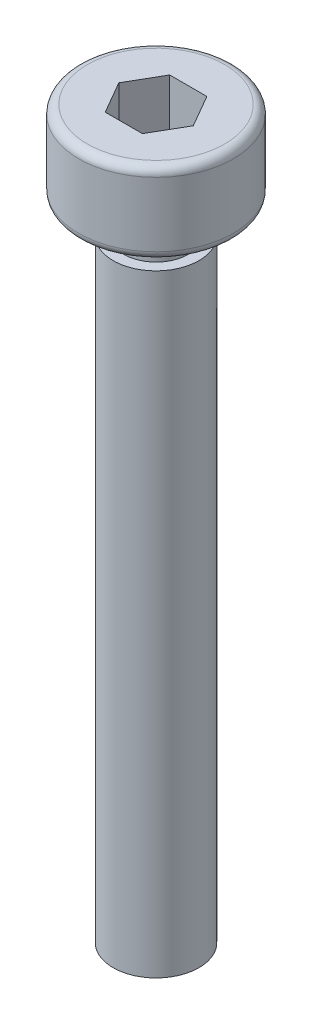
SolidWorks part; units mm, degrees
material "AISI 304"
ref_plane "前视基准面" through (0, 0, 0) normal (0, 0, 1) x (1, 0, 0)
ref_plane "上视基准面" through (0, 0, 0) normal (0, 1, 0) x (1, 0, 0)
ref_plane "右视基准面" through (0, 0, 0) normal (1, 0, 0) x (0, 0, -1)
sketch "草图1" plane through (0, 0, 0) normal (0, 0, 1) x (1, 0, 0)
  line L0 (0, 0) -> (0, 33.8) construction
  line L1 (0, 33.8) -> (-3.2, 33.8)
  line L2 (-3.6, 33.4) -> (-3.6, 30.4)
  line L3 (-3.2, 30) -> (-1.5, 30)
  line L4 (-1.5, 30) -> (-1.5, 28.5)
  line L5 (-1.5, 28.5) -> (-2, 28.5)
  line L6 (-2, 28.5) -> (-2, 0)
  line L7 (-2, 0) -> (0, 0)
  line L8 (0, 0) -> (0, 33.8)
  arc A0 (-3.6, 30.4) -> (-3.2, 30) centre (-3.2, 30.4) ccw
  arc A1 (-3.2, 33.8) -> (-3.6, 33.4) centre (-3.2, 33.4) ccw
  point P11 (-3.6, 30)
  point P14 (-3.6, 33.8)
  dimension "D7" = 0.4
  dimension "D1" = 30
  dimension "D2" = 3.8
  dimension "D3" = 7.2
  dimension "D4" = 4
  dimension "D5" = 1.5
  dimension "D6" = 0.5
revolve "旋转1" add sketch "草图1" angle 360 about L0
cosmetic thread "装饰螺纹线1" parameters "D2"=3.22
sketch "草图2" plane through (0, 33.8, 0) normal (0, 1, 0) x (1, 0, 0)
  line L1 (-0.866, 1.5) -> (-1.7321, 0)
  line L2 (-1.7321, 0) -> (-0.866, -1.5)
  line L3 (-0.866, -1.5) -> (0.866, -1.5)
  line L4 (0.866, -1.5) -> (1.7321, 0)
  line L5 (1.7321, 0) -> (0.866, 1.5)
  line L6 (0.866, 1.5) -> (-0.866, 1.5)
  circle A0 centre (0, 0) radius 1.5 construction
  dimension "D1" = 3
extrude "切除-拉伸1" cut sketch "草图2" against normal blind 2.8
